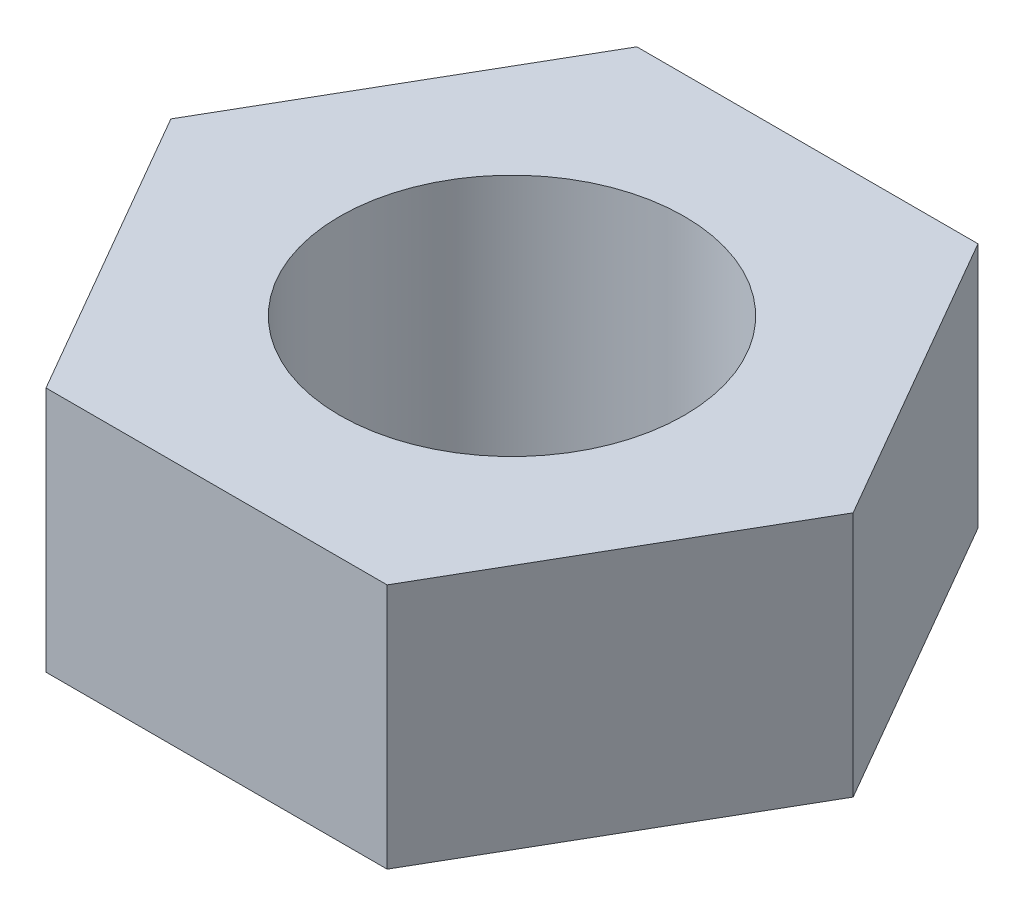
SolidWorks part; units mm, degrees
ref_plane "Front Plane" through (0, 0, 0) normal (0, 0, 1) x (1, 0, 0)
ref_plane "Top Plane" through (0, 0, 0) normal (0, 1, 0) x (1, 0, 0)
ref_plane "Right Plane" through (0, 0, 0) normal (1, 0, 0) x (0, 0, -1)
sketch "Sketch2" plane through (0, 0, 0) normal (0, 1, 0) x (1, 0, 0)
  line L1 (6.9282, 12) -> (-6.9282, 12)
  line L2 (-6.9282, 12) -> (-13.8564, 0)
  line L3 (-13.8564, 0) -> (-6.9282, -12)
  line L4 (-6.9282, -12) -> (6.9282, -12)
  line L5 (6.9282, -12) -> (13.8564, 0)
  line L6 (13.8564, 0) -> (6.9282, 12)
  circle A0 centre (0, 0) radius 12 construction
  circle A1 centre (0, 0) radius 7
  dimension "D2" = 14
  dimension "D1" = 24
extrude "Boss-Extrude1" add sketch "Sketch2" along normal blind 10
